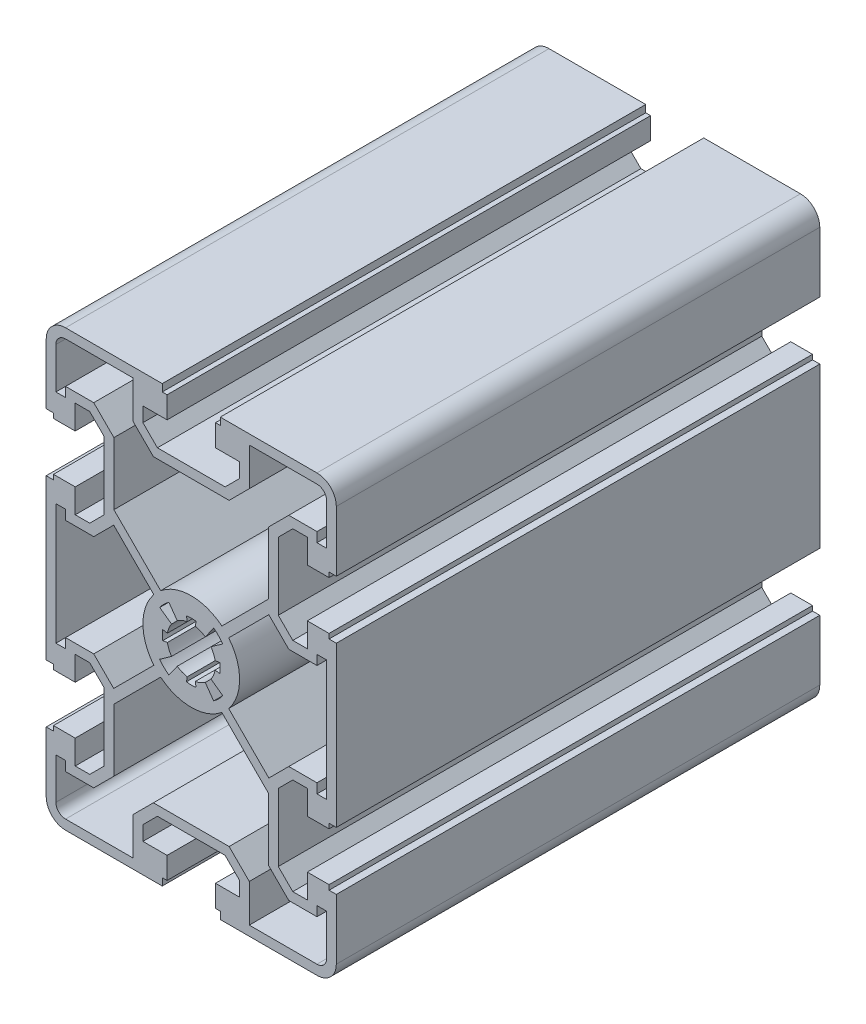
SolidWorks part; units mm, degrees
ref_plane "Ön Düzlem" through (0, 0, 0) normal (0, 0, 1) x (1, 0, 0)
ref_plane "Üst Düzlem" through (0, 0, 0) normal (0, 1, 0) x (1, 0, 0)
ref_plane "Sağ Düzlem" through (0, 0, 0) normal (1, 0, 0) x (0, 0, -1)
ref_plane "Düzlem1" through (0, 0, 100) normal (0, 0, 1) x (1, 0, 0)
sketch "Çizim1" plane through (0, 0, 100) normal (0, 0, 1) x (1, 0, 0)
  line L0 (-28.5, 16.5) -> (-30, 16.5)
  line L1 (-30, 16.5) -> (-30, -16.5)
  line L2 (-30, -16.5) -> (-28.5, -16.5)
  line L3 (-28.5, -16.5) -> (-28.5, -17.5)
  line L4 (-28.5, -17.5) -> (-24, -17.5)
  line L5 (-24, -17.5) -> (-24, -12.5)
  line L6 (-24, -12.5) -> (-21, -12.5)
  line L7 (-21, -12.5) -> (-18, -15.5)
  line L8 (-18, -15.5) -> (-18, -29.5)
  line L9 (-18, -29.5) -> (-21, -32.5)
  line L10 (-21, -32.5) -> (-24, -32.5)
  line L11 (-24, -32.5) -> (-24, -27.5)
  line L12 (-24, -27.5) -> (-28.5, -27.5)
  line L13 (-28.5, -27.5) -> (-28.5, -28.5)
  line L14 (-28.5, -28.5) -> (-30, -28.5)
  line L15 (-30, -28.5) -> (-30, -41)
  line L16 (-26, -45) -> (-6, -45)
  line L17 (-6, -45) -> (-6, -43.5)
  line L18 (-6, -43.5) -> (-5, -43.5)
  line L19 (-5, -43.5) -> (-5, -39)
  line L20 (-5, -39) -> (-10, -39)
  line L21 (-10, -39) -> (-10, -36)
  line L22 (-10, -36) -> (-7, -33)
  line L23 (-7, -33) -> (7, -33)
  line L24 (7, -33) -> (10, -36)
  line L25 (10, -36) -> (10, -39)
  line L26 (10, -39) -> (5, -39)
  line L27 (5, -39) -> (5, -43.5)
  line L28 (5, -43.5) -> (6, -43.5)
  line L29 (6, -43.5) -> (6, -45)
  line L30 (6, -45) -> (26, -45)
  line L31 (30, -41) -> (30, -28.5)
  line L32 (30, -28.5) -> (28.5, -28.5)
  line L33 (28.5, -28.5) -> (28.5, -27.5)
  line L34 (28.5, -27.5) -> (24, -27.5)
  line L35 (24, -27.5) -> (24, -32.5)
  line L36 (24, -32.5) -> (21, -32.5)
  line L37 (21, -32.5) -> (18, -29.5)
  line L38 (18, -29.5) -> (18, -15.5)
  line L39 (18, -15.5) -> (21, -12.5)
  line L40 (21, -12.5) -> (24, -12.5)
  line L41 (24, -12.5) -> (24, -17.5)
  line L42 (24, -17.5) -> (28.5, -17.5)
  line L43 (28.5, -17.5) -> (28.5, -16.5)
  line L44 (28.5, -16.5) -> (30, -16.5)
  line L45 (30, -16.5) -> (30, 16.5)
  line L46 (30, 16.5) -> (28.5, 16.5)
  line L47 (28.5, 16.5) -> (28.5, 17.5)
  line L48 (28.5, 17.5) -> (24, 17.5)
  line L49 (24, 17.5) -> (24, 12.5)
  line L50 (24, 12.5) -> (21, 12.5)
  line L51 (21, 12.5) -> (18, 15.5)
  line L52 (18, 15.5) -> (18, 29.5)
  line L53 (18, 29.5) -> (21, 32.5)
  line L54 (21, 32.5) -> (24, 32.5)
  line L55 (24, 32.5) -> (24, 27.5)
  line L56 (24, 27.5) -> (28.5, 27.5)
  line L57 (28.5, 27.5) -> (28.5, 28.5)
  line L58 (28.5, 28.5) -> (30, 28.5)
  line L59 (30, 28.5) -> (30, 41)
  line L60 (26, 45) -> (6, 45)
  line L61 (6, 45) -> (6, 43.5)
  line L62 (6, 43.5) -> (5, 43.5)
  line L63 (5, 43.5) -> (5, 39)
  line L64 (5, 39) -> (10, 39)
  line L65 (10, 39) -> (10, 36)
  line L66 (10, 36) -> (7, 33)
  line L67 (7, 33) -> (-7, 33)
  line L68 (-7, 33) -> (-10, 36)
  line L69 (-10, 36) -> (-10, 39)
  line L70 (-10, 39) -> (-5, 39)
  line L71 (-5, 39) -> (-5, 43.5)
  line L72 (-5, 43.5) -> (-6, 43.5)
  line L73 (-6, 43.5) -> (-6, 45)
  line L74 (-6, 45) -> (-26, 45)
  line L75 (-30, 41) -> (-30, 28.5)
  line L76 (-30, 28.5) -> (-28.5, 28.5)
  line L77 (-28.5, 28.5) -> (-28.5, 27.5)
  line L78 (-28.5, 27.5) -> (-24, 27.5)
  line L79 (-24, 27.5) -> (-24, 32.5)
  line L80 (-24, 32.5) -> (-21, 32.5)
  line L81 (-21, 32.5) -> (-18, 29.5)
  line L82 (-18, 29.5) -> (-18, 15.5)
  line L83 (-18, 15.5) -> (-21, 12.5)
  line L84 (-21, 12.5) -> (-24, 12.5)
  line L85 (-24, 12.5) -> (-24, 17.5)
  line L86 (-24, 17.5) -> (-28.5, 17.5)
  line L87 (-28.5, 17.5) -> (-28.5, 16.5)
  line L88 (-7.8284, 31) -> (7.8284, 31)
  line L89 (7.8284, 31) -> (12, 35.1716)
  line L90 (12, 35.1716) -> (12, 43)
  line L91 (12, 43) -> (26, 43)
  line L92 (28, 41) -> (28, 32.5)
  line L93 (28, 32.5) -> (26, 32.5)
  line L94 (26, 32.5) -> (26, 34.5)
  line L95 (26, 34.5) -> (20.1716, 34.5)
  line L96 (20.1716, 34.5) -> (16, 30.3284)
  line L97 (16, 30.3284) -> (16, 17.4142)
  line L98 (16, 17.4142) -> (6.3285, 7.7427)
  line L99 (-6.3285, 7.7427) -> (-16, 17.4142)
  line L100 (-16, 17.4142) -> (-16, 30.3284)
  line L101 (-16, 30.3284) -> (-20.1716, 34.5)
  line L102 (-20.1716, 34.5) -> (-26, 34.5)
  line L103 (-26, 34.5) -> (-26, 32.5)
  line L104 (-26, 32.5) -> (-28, 32.5)
  line L105 (-28, 32.5) -> (-28, 41)
  line L106 (-26, 43) -> (-12, 43)
  line L107 (-12, 43) -> (-12, 35.1716)
  line L108 (-12, 35.1716) -> (-7.8284, 31)
  line L109 (7.8284, -31) -> (-7.8284, -31)
  line L110 (-7.8284, -31) -> (-12, -35.1716)
  line L111 (-12, -35.1716) -> (-12, -43)
  line L112 (-12, -43) -> (-26, -43)
  line L113 (-28, -41) -> (-28, -32.5)
  line L114 (-28, -32.5) -> (-26, -32.5)
  line L115 (-26, -32.5) -> (-26, -34.5)
  line L116 (-26, -34.5) -> (-20.1716, -34.5)
  line L117 (-20.1716, -34.5) -> (-16, -30.3284)
  line L118 (-16, -30.3284) -> (-16, -17.4142)
  line L119 (-16, -17.4142) -> (-6.3285, -7.7427)
  line L120 (6.3285, -7.7427) -> (16, -17.4142)
  line L121 (16, -17.4142) -> (16, -30.3284)
  line L122 (16, -30.3284) -> (20.1716, -34.5)
  line L123 (20.1716, -34.5) -> (26, -34.5)
  line L124 (26, -34.5) -> (26, -32.5)
  line L125 (26, -32.5) -> (28, -32.5)
  line L126 (28, -32.5) -> (28, -41)
  line L127 (26, -43) -> (12, -43)
  line L128 (12, -43) -> (12, -35.1716)
  line L129 (12, -35.1716) -> (7.8284, -31)
  line L130 (7.7427, 6.3285) -> (16.0429, 14.6287)
  line L131 (16.0429, 14.6287) -> (20.1716, 10.5)
  line L132 (20.1716, 10.5) -> (26, 10.5)
  line L133 (26, 10.5) -> (26, 12.5)
  line L134 (26, 12.5) -> (28, 12.5)
  line L135 (28, 12.5) -> (28, -12.5)
  line L136 (28, -12.5) -> (26, -12.5)
  line L137 (26, -12.5) -> (26, -10.5)
  line L138 (26, -10.5) -> (20.1716, -10.5)
  line L139 (20.1716, -10.5) -> (16.0429, -14.6287)
  line L140 (16.0429, -14.6287) -> (7.7427, -6.3285)
  line L141 (-7.7427, -6.3285) -> (-16.0429, -14.6287)
  line L142 (-16.0429, -14.6287) -> (-20.1716, -10.5)
  line L143 (-20.1716, -10.5) -> (-26, -10.5)
  line L144 (-26, -10.5) -> (-26, -12.5)
  line L145 (-26, -12.5) -> (-28, -12.5)
  line L146 (-28, -12.5) -> (-28, 12.5)
  line L147 (-28, 12.5) -> (-26, 12.5)
  line L148 (-26, 12.5) -> (-26, 10.5)
  line L149 (-26, 10.5) -> (-20.1716, 10.5)
  line L150 (-20.1716, 10.5) -> (-16.0429, 14.6287)
  line L151 (-16.0429, 14.6287) -> (-7.7427, 6.3285)
  line L152 (4.6354, -6.5202) -> (2.8971, -4.0751)
  line L153 (0.833, -4.9301) -> (0.9996, -5.9162)
  line L154 (-0.9996, -5.9162) -> (-0.833, -4.9301)
  line L155 (-2.8971, -4.0751) -> (-4.6354, -6.5202)
  line L156 (-6.5202, -4.6354) -> (-4.0751, -2.8971)
  line L157 (-4.9301, -0.833) -> (-5.9162, -0.9996)
  line L158 (-5.9162, 0.9996) -> (-4.9301, 0.833)
  line L159 (-4.0751, 2.8971) -> (-6.5202, 4.6354)
  line L160 (-4.6354, 6.5202) -> (-2.8971, 4.0751)
  line L161 (-0.833, 4.9301) -> (-0.9996, 5.9162)
  line L162 (0.9996, 5.9162) -> (0.833, 4.9301)
  line L163 (2.8971, 4.0751) -> (4.6354, 6.5202)
  line L164 (6.5202, 4.6354) -> (4.0751, 2.8971)
  line L165 (4.9301, 0.833) -> (5.9162, 0.9996)
  line L166 (5.9162, -0.9996) -> (4.9301, -0.833)
  line L167 (4.0751, -2.8971) -> (6.5202, -4.6354)
  arc A0 (-30, -41) -> (-26, -45) centre (-26, -41) ccw
  arc A1 (26, -45) -> (30, -41) centre (26, -41) ccw
  arc A2 (30, 41) -> (26, 45) centre (26, 41) ccw
  arc A3 (-26, 45) -> (-30, 41) centre (-26, 41) ccw
  arc A4 (26, 43) -> (28, 41) centre (26, 41) cw
  arc A5 (6.3285, 7.7427) -> (-6.3285, 7.7427) centre (0, 0) ccw
  arc A6 (-28, 41) -> (-26, 43) centre (-26, 41) cw
  arc A7 (-26, -43) -> (-28, -41) centre (-26, -41) cw
  arc A8 (-6.3285, -7.7427) -> (6.3285, -7.7427) centre (0, 0) ccw
  arc A9 (28, -41) -> (26, -43) centre (26, -41) cw
  arc A10 (7.7427, -6.3285) -> (7.7427, 6.3285) centre (0, 0) ccw
  arc A11 (-7.7427, 6.3285) -> (-7.7427, -6.3285) centre (0, 0) ccw
  arc A12 (6.5202, -4.6354) -> (4.6354, -6.5202) centre (0, 0) cw
  arc A13 (2.8971, -4.0751) -> (0.833, -4.9301) centre (0, 0) cw
  arc A14 (0.9996, -5.9162) -> (-0.9996, -5.9162) centre (0, 0) cw
  arc A15 (-0.833, -4.9301) -> (-2.8971, -4.0751) centre (0, 0) cw
  arc A16 (-4.6354, -6.5202) -> (-6.5202, -4.6354) centre (0, 0) cw
  arc A17 (-4.0751, -2.8971) -> (-4.9301, -0.833) centre (0, 0) cw
  arc A18 (-5.9162, -0.9996) -> (-5.9162, 0.9996) centre (0, 0) cw
  arc A19 (-4.9301, 0.833) -> (-4.0751, 2.8971) centre (0, 0) cw
  arc A20 (-6.5202, 4.6354) -> (-4.6354, 6.5202) centre (0, 0) cw
  arc A21 (-2.8971, 4.0751) -> (-0.833, 4.9301) centre (0, 0) cw
  arc A22 (-0.9996, 5.9162) -> (0.9996, 5.9162) centre (0, 0) cw
  arc A23 (0.833, 4.9301) -> (2.8971, 4.0751) centre (0, 0) cw
  arc A24 (4.6354, 6.5202) -> (6.5202, 4.6354) centre (0, 0) cw
  arc A25 (4.0751, 2.8971) -> (4.9301, 0.833) centre (0, 0) cw
  arc A26 (5.9162, 0.9996) -> (5.9162, -0.9996) centre (0, 0) cw
  arc A27 (4.9301, -0.833) -> (4.0751, -2.8971) centre (0, 0) cw
extrude "Yükseklik-Ekstrüzyon1" add sketch "Çizim1" against normal blind 100
